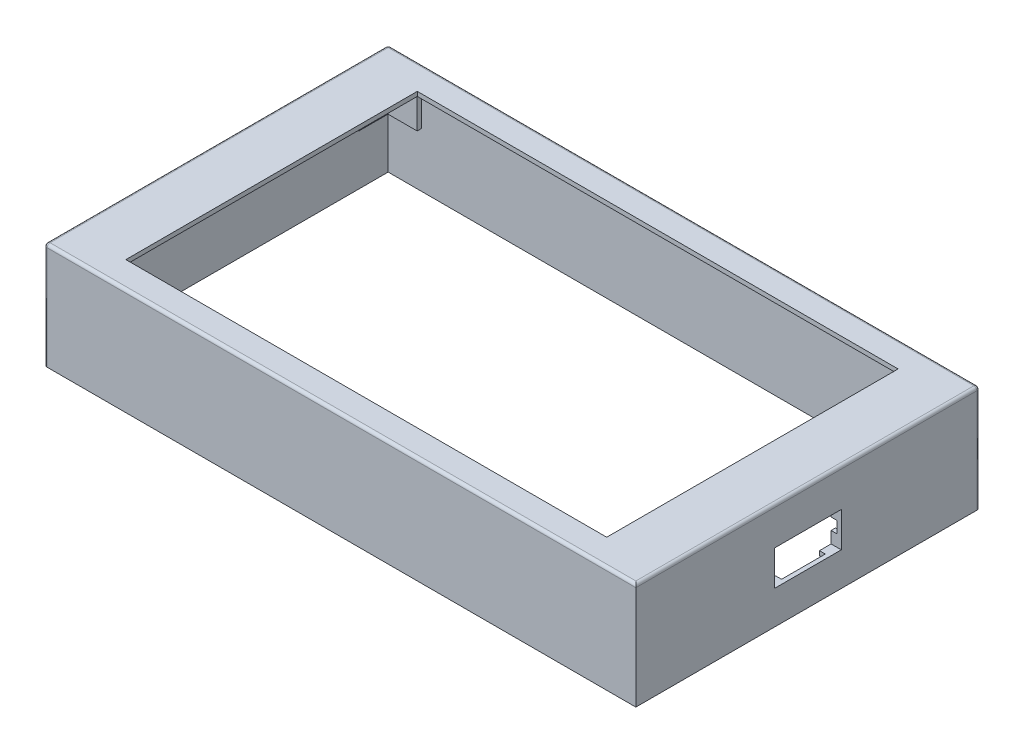
SolidWorks part; units mm, degrees
ref_plane "前视基准面" through (0, 0, 0) normal (0, 0, 1) x (1, 0, 0)
ref_plane "上视基准面" through (0, 0, 0) normal (0, 1, 0) x (1, 0, 0)
ref_plane "右视基准面" through (0, 0, 0) normal (1, 0, 0) x (0, 0, -1)
other "Configuration Table"
sketch "草图1" plane through (0, 0, 0) normal (0, 1, 0) x (1, 0, 0)
  line L1 (-82.5, 50) -> (82.5, 50) construction
  line L2 (-82.5, 50) -> (-82.5, -50) construction
  line L3 (-82.5, -50) -> (82.5, -50) construction
  line L4 (82.5, 50) -> (82.5, -50) construction
  line L5 (-82.5, 50) -> (82.5, -50) construction
  line L6 (-82.5, -50) -> (82.5, 50) construction
  line L7 (100, -57.5) -> (-100, -57.5)
  line L8 (100, -57.5) -> (100, 57.5)
  line L9 (100, 57.5) -> (-100, 57.5)
  line L10 (-100, -57.5) -> (-100, 57.5)
  line L11 (100, -57.5) -> (-100, 57.5) construction
  line L12 (100, 57.5) -> (-100, -57.5) construction
  point P0 (0, 0)
  point P6 (0, 0)
  dimension "D1" = 100
  dimension "D2" = 165
  dimension "D3" = 200
  dimension "D4" = 115
extrude "凸台-拉伸35mm" add sketch "草图1" along normal blind 35
ref_plane "基准面1" through (0, 35, 0) normal (0, 1, 0) x (1, 0, 0)
sketch "草图2" plane through (0, 35, 0) normal (0, 1, 0) x (1, 0, 0)
  line L0 (82.5, 50) -> (82.5, -50) construction
  line L1 (-82.5, -50) -> (82.5, -50) construction
  line L2 (-82.5, 50) -> (-82.5, -50) construction
  line L3 (-82.5, 50) -> (82.5, 50) construction
  line L4 (82.5, 50) -> (82.5, -50)
  line L5 (-82.5, -50) -> (82.5, -50)
  line L6 (-82.5, 50) -> (-82.5, -50)
  line L7 (-82.5, 50) -> (82.5, 50)
shell "抽壳3" thickness 1.5
extrude "切除-拉伸7" cut sketch "草图2" along normal blind 1.5
ref_plane "基准面2" through (-100, 0, 0) normal (1, 0, 0) x (0, 0, -1)
sketch "草图3" plane through (-100, 0, 0) normal (1, 0, 0) x (0, 0, -1)
  line L1 (50, 36.5) -> (-50, 36.5) construction
  line L2 (50, 36.5) -> (-50, 36.5) construction
  line L3 (37.9694, 27.5) -> (-16.0374, 27.5) construction
  line L4 (37.9694, 17.5) -> (-20.8388, 17.5) construction
  line L5 (50, 36.5) -> (50, 13.3792) construction
  line L6 (20, 5.8143) -> (20, 79.2673) construction
  line L7 (20, 17.5) -> (20, 27.5)
  line L8 (4, 27.5) -> (4, 17.5)
  line L9 (4, 17.5) -> (20, 17.5)
  line L10 (20, 27.5) -> (4, 27.5)
  dimension "D1" = 9
  dimension "D2" = 10
  dimension "D3" = 30
  dimension "D4" = 16
extrude "切除-拉伸8" cut sketch "草图3" against normal blind 1.5
ref_plane "基准面3" through (100, 0, 0) normal (-1, 0, 0) x (0, 0, 1)
sketch "草图4" plane through (100, 0, 0) normal (-1, 0, 0) x (0, 0, 1)
  line L0 (50, 36.5) -> (-50, 36.5) construction
  line L1 (50, 36.5) -> (-50, 36.5) construction
  line L2 (-59, 36.5) -> (-59, 0) construction
  line L3 (-59, 36.5) -> (-59, 0) construction
  line L4 (-59, 18.25) -> (56.2233, 18.25) construction
  line L5 (0, 36.5) -> (0, -21.6986) construction
  line L6 (-11.5, 11.5) -> (11.5, 23.5) construction
  line L7 (-11.5, 23.5) -> (11.5, 23.5)
  line L8 (-11.5, 23.5) -> (-11.5, 11.5)
  line L9 (-11.5, 11.5) -> (11.5, 11.5)
  line L10 (11.5, 23.5) -> (11.5, 11.5)
  line L11 (-11.5, 23.5) -> (11.5, 11.5) construction
  point P13 (0, 17.5)
  dimension "D1" = 58.1986
  dimension "D2" = 13
  dimension "D3" = 12
  dimension "D4" = 23
extrude "切除-拉伸9" cut sketch "草图4" against normal blind 1.5
ref_plane "基准面4" through (0, 35, 0) normal (0, -1, 0) x (-1, 0, 0)
sketch "草图6" plane through (0, 35, 0) normal (0, -1, 0) x (-1, 0, 0)
  line L0 (-44.1359, 0) -> (40.9262, 0) construction
  line L1 (-95.25, -52.7) -> (95.25, -52.7) construction
  line L2 (-95.25, -52.7) -> (-95.25, 52.7) construction
  line L3 (-95.25, 52.7) -> (95.25, 52.7) construction
  line L4 (95.25, -52.7) -> (95.25, 52.7) construction
  line L5 (-95.25, -52.7) -> (95.25, 52.7) construction
  line L6 (-95.25, 52.7) -> (95.25, -52.7) construction
  line L7 (0, 35.4902) -> (0, -35.4611) construction
  line L8 (-95.25, 52.7) -> (-85.25, 52.7)
  line L9 (-85.25, 52.7) -> (-85.25, 54.2)
  line L10 (-85.25, 54.2) -> (-96.75, 54.2)
  line L11 (-96.75, 54.2) -> (-96.75, 42.7)
  line L12 (-96.75, 42.7) -> (-95.25, 42.7)
  line L13 (-95.25, 42.7) -> (-95.25, 52.7)
  line L14 (-96.75, -42.7) -> (-95.25, -42.7)
  line L15 (-85.25, -52.7) -> (-85.25, -54.2)
  line L16 (-96.75, -54.2) -> (-96.75, -42.7)
  line L17 (-85.25, -54.2) -> (-96.75, -54.2)
  line L18 (-95.25, -52.7) -> (-85.25, -52.7)
  line L19 (-95.25, -42.7) -> (-95.25, -52.7)
  line L20 (85.25, -52.7) -> (85.25, -54.2)
  line L21 (85.25, -54.2) -> (96.75, -54.2)
  line L22 (95.25, -52.7) -> (85.25, -52.7)
  line L23 (95.25, -42.7) -> (95.25, -52.7)
  line L24 (96.75, -54.2) -> (96.75, -42.7)
  line L25 (96.75, -42.7) -> (95.25, -42.7)
  line L26 (85.25, 52.7) -> (85.25, 54.2)
  line L27 (96.75, 42.7) -> (95.25, 42.7)
  line L28 (95.25, 52.7) -> (85.25, 52.7)
  line L29 (95.25, 42.7) -> (95.25, 52.7)
  line L30 (96.75, 54.2) -> (96.75, 42.7)
  line L31 (85.25, 54.2) -> (96.75, 54.2)
  point P0 (0, 0)
  dimension "D1" = 190.5
  dimension "D2" = 105.4
  dimension "D3" = 1.5
  dimension "D4" = 1.5
  dimension "D5" = 10
  dimension "D6" = 10
extrude "凸台-拉伸1" add sketch "草图6" along normal blind 13
ref_plane "基准面5" through (100, 0, 0) normal (-1, 0, 0) x (0, 0, 1)
sketch "草图7" plane through (100, 0, 0) normal (-1, 0, 0) x (0, 0, 1)
  line L0 (57.5, 35) -> (-57.5, 35) construction
  line L1 (-11.5, 11.5) -> (11.5, 11.5) construction
  line L2 (11.5, 23.5) -> (11.5, 11.5) construction
  line L3 (-11.5, 23.5) -> (11.5, 23.5) construction
  line L4 (-11.5, 23.5) -> (-11.5, 11.5) construction
  line L5 (57.5, 35) -> (-57.5, 35) construction
  line L6 (-11.5, 11.5) -> (11.5, 11.5) construction
  line L7 (11.5, 23.5) -> (11.5, 11.5) construction
  line L8 (-11.5, 23.5) -> (11.5, 23.5) construction
  line L9 (-11.5, 23.5) -> (-11.5, 11.5) construction
  line L10 (50, 36.5) -> (-50, 36.5) construction
  line L11 (50, 36.5) -> (-50, 36.5) construction
  line L12 (13, 15.5) -> (11.5, 15.5)
  line L13 (-7.5, 23.5) -> (-7.5, 25)
  line L14 (-7.5, 25) -> (-13, 25)
  line L15 (-13, 25) -> (-13, 19.5)
  line L16 (-13, 19.5) -> (-11.5, 19.5)
  line L17 (-11.5, 19.5) -> (-11.5, 23.5)
  line L18 (-11.5, 23.5) -> (-7.5, 23.5)
  line L19 (0, 23.5) -> (0, 11.5) construction
  line L20 (-3.0917, 17.5) -> (3.5005, 17.5) construction
  line L21 (7.5, 23.5) -> (7.5, 25)
  line L22 (11.5, 23.5) -> (7.5, 23.5)
  line L23 (11.5, 19.5) -> (11.5, 23.5)
  line L24 (13, 19.5) -> (11.5, 19.5)
  line L25 (13, 25) -> (13, 19.5)
  line L26 (7.5, 25) -> (13, 25)
  line L27 (13, 10) -> (13, 15.5)
  line L28 (11.5, 15.5) -> (11.5, 11.5)
  line L29 (11.5, 11.5) -> (7.5, 11.5)
  line L30 (7.5, 11.5) -> (7.5, 10)
  line L31 (7.5, 10) -> (13, 10)
  line L32 (-7.5, 11.5) -> (-7.5, 10)
  line L33 (-11.5, 11.5) -> (-7.5, 11.5)
  line L34 (-11.5, 15.5) -> (-11.5, 11.5)
  line L35 (-13, 15.5) -> (-11.5, 15.5)
  line L36 (-13, 10) -> (-13, 15.5)
  line L37 (-7.5, 10) -> (-13, 10)
  dimension "D1" = 1.5
  dimension "D2" = 1.5
  dimension "D3" = 4
  dimension "D4" = 4
extrude "凸台-拉伸2" add sketch "草图7" along normal blind 2
fillet "圆角2" radius 1 8 edges at (100, 17.5, 57.5) (0, 36.5, 59) (-101.5, 18.25, 59) (101.5, 36.5, 0) (101.5, 18.25, -59) (-101.5, 36.5, 0) (-101.5, 18.25, -59) (0, 36.5, -59)
